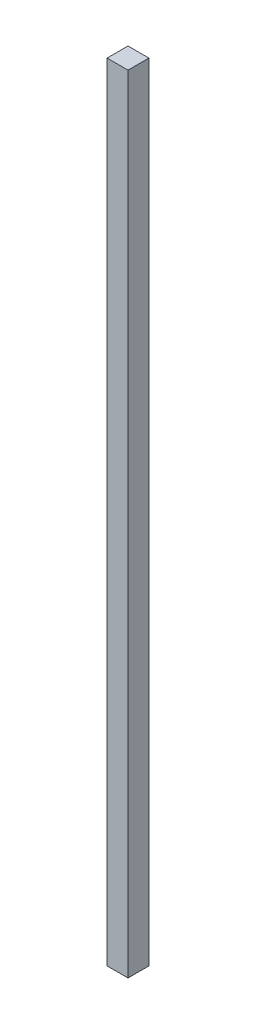
SolidWorks part; units mm, degrees
ref_plane "Front Plane" through (0, 0, 0) normal (0, 0, 1) x (1, 0, 0)
ref_plane "Top Plane" through (0, 0, 0) normal (0, 1, 0) x (1, 0, 0)
ref_plane "Right Plane" through (0, 0, 0) normal (1, 0, 0) x (0, 0, -1)
sketch "Sketch1" plane through (0, 0, 0) normal (0, 1, 0) x (1, 0, 0)
  line L1 (-39.8355, 18.6136) -> (-14.4355, 18.6136)
  line L2 (-39.8355, 18.6136) -> (-39.8355, -6.7864)
  line L3 (-39.8355, -6.7864) -> (-14.4355, -6.7864)
  line L4 (-14.4355, 18.6136) -> (-14.4355, -6.7864)
  dimension "D1" = 25.4
  dimension "D2" = 25.4
extrude "Boss-Extrude1" add sketch "Sketch1" along normal blind 955
